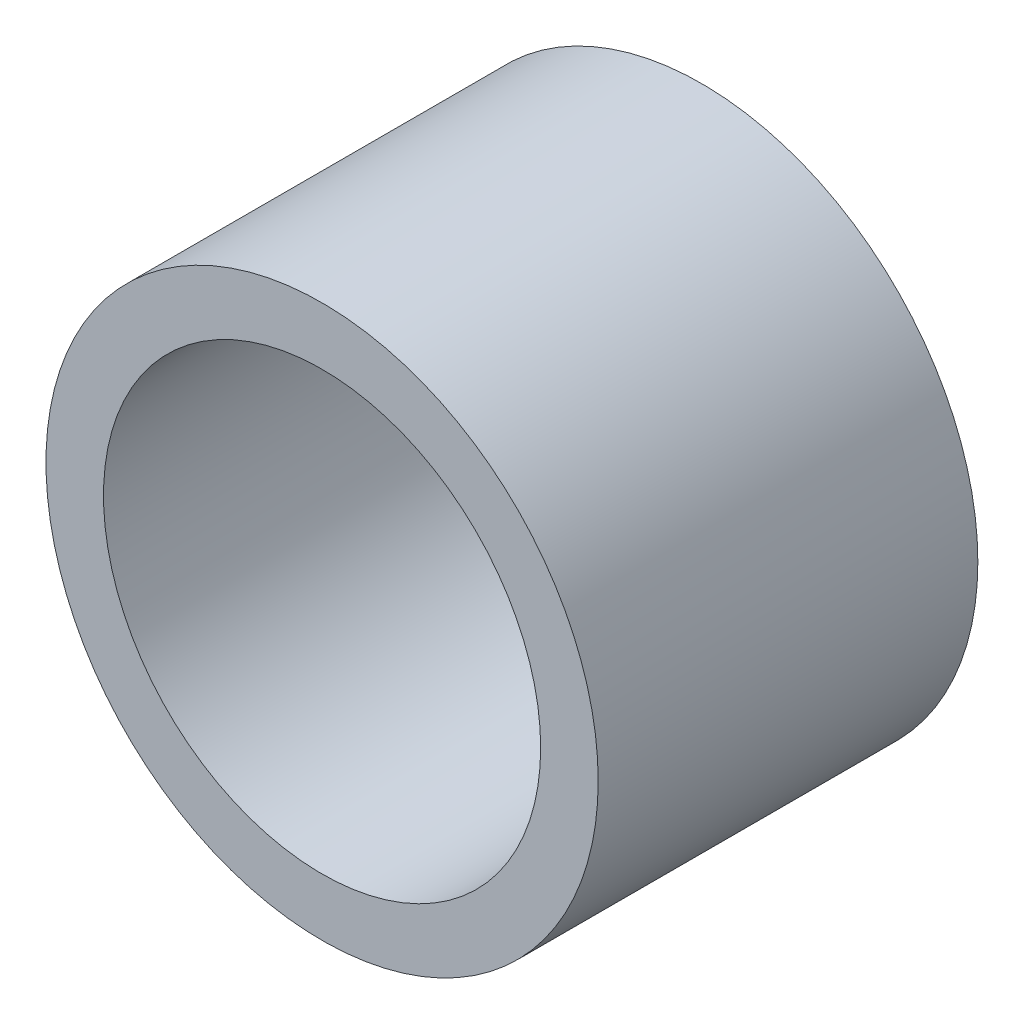
SolidWorks part; units mm, degrees
ref_plane "Front Plane" through (0, 0, 0) normal (1, 0, 0) x (0, 1, 0)
ref_plane "Top Plane" through (0, 0, 0) normal (0, 0, 1) x (0, 1, 0)
ref_plane "Right Plane" through (0, 0, 0) normal (0, 1, 0) x (-1, 0, 0)
sketch "Sketch1" plane through (0, 0, 0) normal (0, 0, 1) x (0, 1, 0)
  circle A0 centre (0, 0) radius 12
  circle A1 centre (0, 0) radius 9.5
  dimension "D1" = 24
  dimension "D2" = 19
extrude "Boss-Extrude1" add sketch "Sketch1" along normal blind 16.5
scale "Scale1" scale about centroid uniform scaling yes scale factor 0.75
scale "Scale2" scale about centroid uniform scaling yes scale factor 0.85
